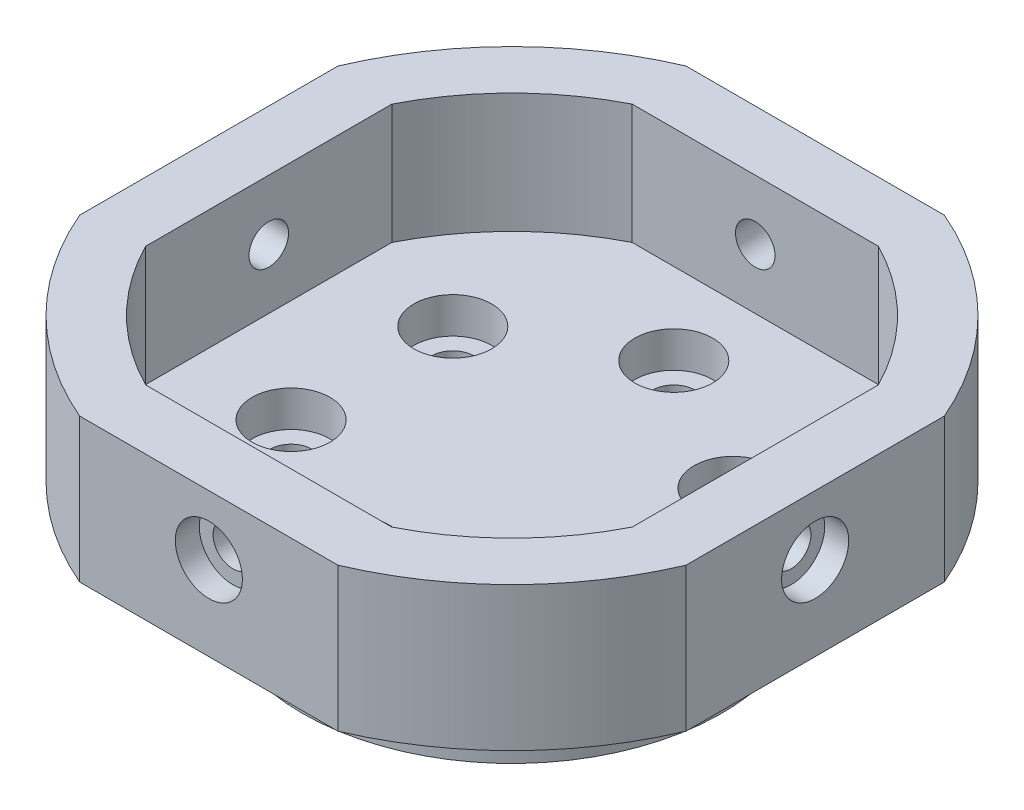
SolidWorks part; units mm, degrees
ref_plane "前视基准面" through (0, 0, 0) normal (0, 0, 1) x (1, 0, 0)
ref_plane "上视基准面" through (0, 0, 0) normal (0, 1, 0) x (1, 0, 0)
ref_plane "右视基准面" through (0, 0, 0) normal (1, 0, 0) x (0, 0, -1)
sketch "草图1" plane through (0, 0, 0) normal (0, 1, 0) x (1, 0, 0)
  circle A0 centre (0, 0) radius 17.5
  circle A1 centre (0, 0) radius 13.5 construction
  circle A2 centre (0, 13.5) radius 1.75
  circle A3 centre (11.6913, 6.75) radius 1.75
  circle A4 centre (11.6913, -6.75) radius 1.75
  circle A5 centre (0, -13.5) radius 1.75
  circle A6 centre (-11.6913, -6.75) radius 1.75
  circle A7 centre (-11.6913, 6.75) radius 1.75
  point P18 (0, 0)
  dimension "D1" = 35
  dimension "D2" = 27
  dimension "D3" = 3.5
  dimension "D4" = 6
extrude "凸台-拉伸1" add sketch "草图1" along normal blind 10
sketch "草图2" plane through (0, 10, 0) normal (0, 1, 0) x (1, 0, 0)
  circle A0 centre (0, 0) radius 25
  circle A1 centre (0, 0) radius 17.5
  dimension "D1" = 50
  dimension "D2" = 35
extrude "凸台-拉伸2" add sketch "草图2" against normal blind 2
sketch "草图3" plane through (0, 10, 0) normal (0, 1, 0) x (1, 0, 0)
  circle A0 centre (0, 13.5) radius 3.25
  circle A1 centre (11.6913, 6.75) radius 3.25
  circle A2 centre (11.6913, -6.75) radius 3.25
  circle A3 centre (0, -13.5) radius 3.25
  circle A4 centre (-11.6913, -6.75) radius 3.25
  circle A5 centre (-11.6913, 6.75) radius 3.25
  point P15 (0, 0)
  dimension "D1" = 6.5
  dimension "D2" = 6
extrude "切除-拉伸1" cut sketch "草图3" against normal blind 3
sketch "草图4" plane through (0, 10, 0) normal (0, 1, 0) x (1, 0, 0)
  line L4 (-10.27, 20.3) -> (10.27, 20.3)
  line L5 (-20.3, 10.27) -> (-20.3, -10.27)
  line L6 (-10.27, -20.3) -> (10.27, -20.3)
  line L7 (20.3, 10.27) -> (20.3, -10.27)
  line L8 (-10.7778, 25.3) -> (10.7778, 25.3)
  line L9 (-25.3, 10.7778) -> (-25.3, -10.7778)
  line L10 (-10.7778, -25.3) -> (10.7778, -25.3)
  line L11 (25.3, 10.7778) -> (25.3, -10.7778)
  arc A4 (-25.3, -10.7778) -> (-10.7778, -25.3) centre (0, 0) ccw
  arc A5 (-10.27, 20.3) -> (-20.3, 10.27) centre (0, 0) ccw construction
  arc A6 (-10.27, 20.3) -> (-20.3, 10.27) centre (0, 0) ccw
  arc A7 (20.3, 10.27) -> (10.27, 20.3) centre (0, 0) ccw construction
  arc A8 (20.3, 10.27) -> (10.27, 20.3) centre (0, 0) ccw
  arc A9 (10.27, -20.3) -> (20.3, -10.27) centre (0, 0) ccw construction
  arc A10 (10.27, -20.3) -> (20.3, -10.27) centre (0, 0) ccw
  arc A11 (-20.3, -10.27) -> (-10.27, -20.3) centre (0, 0) ccw construction
  arc A12 (-20.3, -10.27) -> (-10.27, -20.3) centre (0, 0) ccw
  arc A13 (25.3, 10.7778) -> (10.7778, 25.3) centre (0, 0) ccw
  arc A14 (10.7778, -25.3) -> (25.3, -10.7778) centre (0, 0) ccw
  arc A15 (-10.7778, 25.3) -> (-25.3, 10.7778) centre (0, 0) ccw
  dimension "D1" = 20.3
  dimension "D6" = 55
  dimension "D7" = 45.5
  dimension "D2" = 20.3
  dimension "D3" = 20.3
  dimension "D4" = 20.3
  dimension "D5" = 5
  dimension "D8" = 5
  dimension "D9" = 5
  dimension "D10" = 5
extrude "凸台-拉伸3" add sketch "草图4" along normal blind 10 and the other way blind 2
sketch "草图6" plane through (0, 0, 25.3) normal (0, 0, 1) x (1, 0, 0)
  line L0 (-10.7778, 20) -> (10.7778, 20) construction
  line L1 (0, 0) -> (0, 20) construction
  line L2 (-17.5, 0) -> (17.5, 0) construction
  circle A0 centre (0, 15) radius 1.65
  dimension "D2" = 3.3
  dimension "D1" = 5
extrude "切除-拉伸2" cut sketch "草图6" against normal mid plane 109
sketch "草图7" plane through (25.3, 0, 0) normal (1, 0, 0) x (0, 0, -1)
  line L0 (-10.7778, 20) -> (10.7778, 20) construction
  line L1 (0, 20) -> (0, 0) construction
  circle A0 centre (0, 15) radius 1.65
  dimension "D1" = 3.3
  dimension "D2" = 5
extrude "切除-拉伸3" cut sketch "草图7" against normal mid plane 109
sketch "草图8" plane through (25.3, 0, 0) normal (1, 0, 0) x (0, 0, -1)
  circle A0 centre (0, 15) radius 2.8
  dimension "D1" = 5.6
extrude "切除-拉伸4" cut sketch "草图8" against normal blind 2
sketch "草图9" plane through (0, 0, -25.3) normal (0, 0, -1) x (-1, 0, 0)
  circle A0 centre (0, 15) radius 2.8
  dimension "D1" = 5.6
extrude "切除-拉伸5" cut sketch "草图9" against normal blind 2
sketch "草图10" plane through (-25.3, 0, 0) normal (-1, 0, 0) x (0, 0, 1)
  circle A0 centre (0, 15) radius 2.8
  dimension "D1" = 5.6
extrude "切除-拉伸6" cut sketch "草图10" against normal blind 2 contours A0
sketch "草图11" plane through (0, 0, 25.3) normal (0, 0, 1) x (1, 0, 0)
  circle A0 centre (0, 15) radius 2.8
  dimension "D1" = 5.6
extrude "切除-拉伸7" cut sketch "草图11" against normal blind 2
